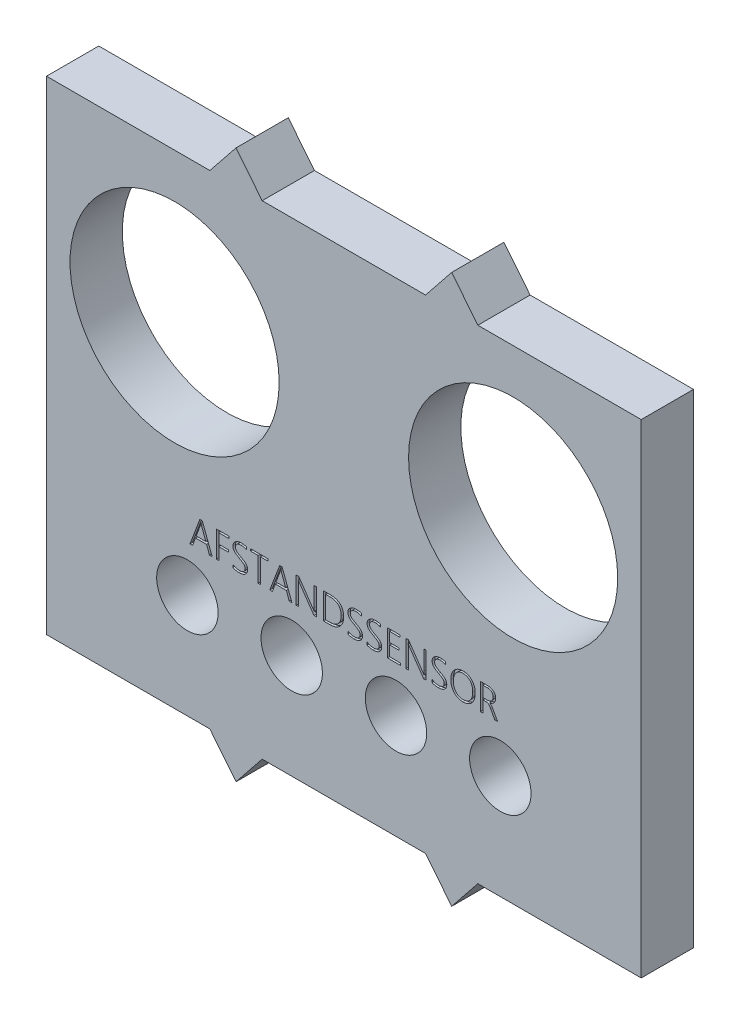
SolidWorks part; units mm, degrees
ref_plane "Front Plane" through (0, 0, 0) normal (0, 0, 1) x (1, 0, 0)
ref_plane "Top Plane" through (0, 0, 0) normal (0, 1, 0) x (1, 0, 0)
ref_plane "Right Plane" through (0, 0, 0) normal (1, 0, 0) x (0, 0, -1)
sketch "Sketch1" plane through (0, 0, 0) normal (0, 0, 1) x (1, 0, 0)
  line L0 (22.75, 37) -> (22.75, 14.7203) construction
  line L1 (0, 0) -> (45.5, 0)
  line L2 (0, 0) -> (0, 37)
  line L3 (0, 37) -> (45.5, 37)
  line L4 (45.5, 0) -> (45.5, 37)
  line L5 (12.5, 37) -> (14.5, 39.5)
  line L6 (14.5, 39.5) -> (16.5, 37)
  line L7 (31, 39.5) -> (29, 37)
  line L8 (33, 37) -> (31, 39.5)
  line L9 (0, 18.5) -> (57.9593, 18.5) construction
  line L10 (33, 0) -> (31, -2.5)
  line L11 (31, -2.5) -> (29, 0)
  line L12 (14.5, -2.5) -> (16.5, 0)
  line L13 (12.5, 0) -> (14.5, -2.5)
  point P9 (22.75, 37)
  point P16 (0, 18.5)
  point P17 (32, 38.25)
  point P18 (32, -1.25)
  dimension "D1" = 37
  dimension "D2" = 45.5
  dimension "D3" = 16.5
  dimension "D4" = 2.5
  dimension "D5" = 4
extrude "Basis" add sketch "Sketch1" along normal blind 4 contours L1 L4 L3 L2 | L6 L5 L3 | L3 L8 L7 | L1 L13 L12 | L11 L10 L1
sketch "Sketch2" [suppressed] plane through (0, 0, 4) normal (0, 0, 1) x (1, 0, 0)
  line L0 (16.5, 37) -> (29, 37) construction
  circle A0 centre (22.75, 23) radius 6.8
  point P5 (22.75, 37)
  dimension "D1" = 13.6
  dimension "D2" = 14
extrude "Camera gat " [suppressed] cut sketch "Sketch2" against normal up to surface (4 mm away)
sketch "Sketch5" [suppressed] plane through (0, 0, 4) normal (0, 0, 1) x (1, 0, 0)
  line L0 (8.6574, 7.1957) -> (36.8426, 7.1957) construction
  line L1 (16.5, 37) -> (29, 37) construction
  text T0 "camera" font "Yu Gothic UI Semilight" height 3.5
  point P2 (22.75, 7.1957)
  point P5 (22.75, 37)
extrude "Cut-Extrude4" [suppressed] cut sketch "Sketch5" against normal blind 0.2
sketch "Sketch3" plane through (0, 0, 4) normal (0, 0, 1) x (1, 0, 0)
  line L0 (22.75, 37) -> (22.75, 0) construction
  line L1 (16.5, 37) -> (29, 37) construction
  line L2 (16.5, 0) -> (29, 0) construction
  line L3 (0, 37) -> (12.5, 37) construction
  circle A0 centre (9.8, 25.6) radius 8
  circle A1 centre (35.7, 25.6) radius 8
  dimension "D3" = 16
  dimension "D1" = 11.4
  dimension "D2" = 25.9
extrude "HR04 gat " cut sketch "Sketch3" against normal up to surface (4 mm away) up to face at (22.75, 18.5, 0)
sketch "Sketch4" [suppressed] plane through (0, 0, 4) normal (0, 0, 1) x (1, 0, 0)
  line L0 (7.7992, 12.9938) -> (37.7008, 12.9938) construction
  line L1 (16.5, 37) -> (29, 37) construction
  text T0 "AFSTAND SENSOR" font "Yu Gothic UI Semilight" height 3.5
  point P5 (22.75, 12.9938)
  point P8 (22.75, 37)
extrude "Afstand sensor" [suppressed] cut sketch "Sketch4" against normal blind 0.2
sketch "Sketch6" [suppressed] plane through (0, 0, 4) normal (0, 0, 1) x (1, 0, 0)
  line L4 (16.5, 37) -> (29, 37) construction
  point P0 (22.75, 31.8)
  point P3 (22.75, 37)
  line B0 (9.1, 31.8) -> (36.4, 31.8)
  line B1 (9.1, 31.8) -> (9.1, 16.3191)
  line B2 (9.1, 16.3191) -> (36.4, 16.3191)
  line B3 (36.4, 31.8) -> (36.4, 16.3191)
  circle B4 centre (11.1, 34.0981) radius 1.5
  circle B5 centre (34.4, 34.0981) radius 1.5
  circle B6 centre (34.4, 10.2981) radius 1.5
  circle B7 centre (11.1, 10.2981) radius 1.5
  dimension "D1" = 5.2
sketch_block_instance "Block1-1" [suppressed]
sketch_block "Block1" parameters "D1"=3, "D2"=3, "D3"=3, "D4"=3
extrude "Cut-Extrude5" [suppressed] cut sketch "Sketch6" against normal up to surface (4 mm away)
sketch "Sketch7" [suppressed] plane through (0, 0, 4) normal (0, 0, 1) x (1, 0, 0)
  line L0 (-2.0092, 11.0348) -> (47.5092, 11.0348) construction
  line L1 (16.5, 37) -> (29, 37) construction
  text T0 "oled scherm " font "Yu Gothic UI Semilight" height 3.5
  point P4 (22.75, 37)
  point P5 (22.75, 11.0348)
extrude "Cut-Extrude6" [suppressed] cut sketch "Sketch7" against normal blind 0.2
sketch "Sketch9" plane through (0, 0, 4) normal (0, 0, 1) x (1, 0, 0)
  line L0 (3.0601, 11.5) -> (42.4399, 11.5) construction
  line L1 (16.5, 0) -> (29, 0) construction
  text T0 "AFSTANDSSENSOR" font "Yu Gothic UI Semilight" height 2
  point P6 (22.75, 11.5)
  point P9 (22.75, 0)
  dimension "D1" = 11.5
extrude "Cut-Extrude8" cut sketch "Sketch9" against normal blind 0.2
sketch "Sketch10" plane through (0, 0, 4) normal (0, 0, 1) x (1, 0, 0)
  line L0 (45.5, 0) -> (45.5, 8) construction
  line L1 (45.5, 0) -> (45.5, 37) construction
  line L2 (45.5, 8) -> (34.72, 8) construction
  line L3 (26.74, 8) -> (18.76, 8) construction
  line L4 (18.76, 8) -> (10.78, 8) construction
  line L5 (10.78, 8) -> (0, 8) construction
  line L6 (0, 0) -> (0, 37) construction
  line L7 (26.74, 8) -> (34.72, 8) construction
  circle A0 centre (10.78, 8) radius 2.35
  circle A1 centre (18.76, 8) radius 2.35
  circle A2 centre (26.74, 8) radius 2.35
  circle A3 centre (34.72, 8) radius 2.35
  dimension "D1" = 4.7
  dimension "D2" = 7.98
  dimension "D3" = 8
extrude "Sonar" cut sketch "Sketch10" against normal blind 10
